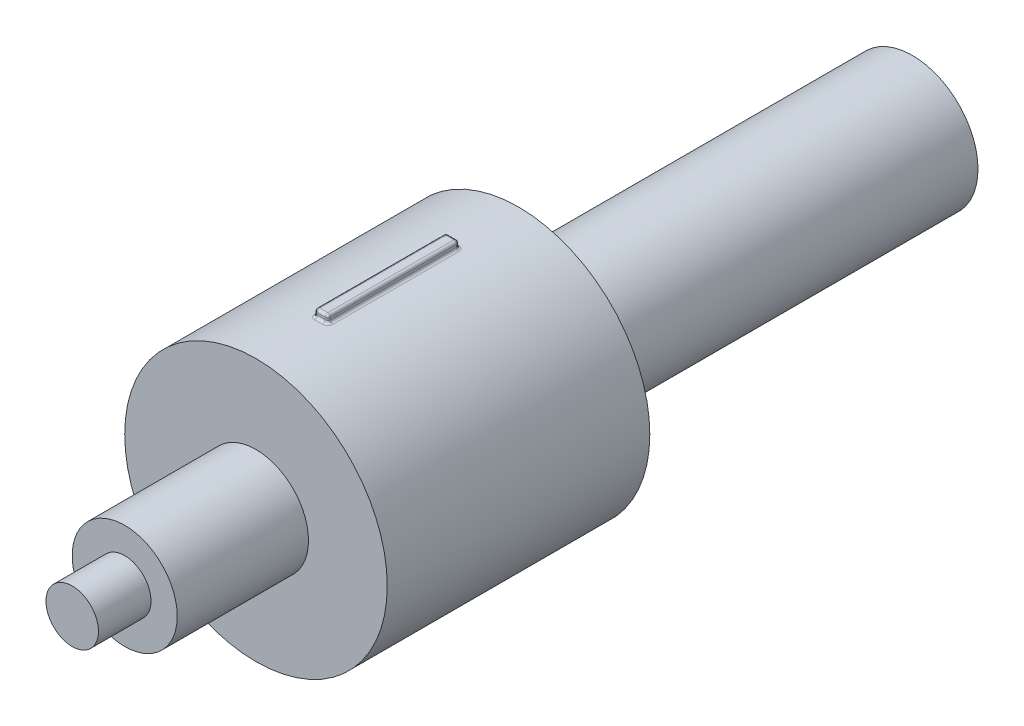
SolidWorks part; units mm, degrees
ref_plane "Front Plane" through (0, 0, 0) normal (0, 0, 1) x (1, 0, 0)
ref_plane "Top Plane" through (0, 0, 0) normal (0, 1, 0) x (1, 0, 0)
ref_plane "Right Plane" through (0, 0, 0) normal (1, 0, 0) x (0, 0, -1)
sketch "Sketch1" plane through (0, 0, 0) normal (0, 0, 1) x (1, 0, 0)
  circle A0 centre (0, 0) radius 5
extrude "Boss-Extrude1" add sketch "Sketch1" along normal blind 30
sketch "Sketch2" plane through (0, 0, 30) normal (0, 0, 1) x (1, 0, 0)
  circle A0 centre (0, 0) radius 10
extrude "Boss-Extrude2" add sketch "Sketch2" along normal blind 20
sketch "Sketch3" plane through (0, 0, 50) normal (0, 0, 1) x (1, 0, 0)
  circle A0 centre (0, 0) radius 4
extrude "Boss-Extrude3" add sketch "Sketch3" along normal blind 10
sketch "Sketch4" plane through (0, 0, 60) normal (0, 0, 1) x (1, 0, 0)
  circle A0 centre (0, 0) radius 2
extrude "Boss-Extrude4" add sketch "Sketch4" along normal blind 4
sketch "Sketch5" plane through (0, 0, 30) normal (0, 0, -1) x (-1, 0, 0)
  line L1 (-0.4647, 10.5602) -> (0.5353, 10.5602)
  line L2 (-0.4647, 10.5602) -> (-0.4647, 9.9637)
  line L4 (0.5353, 10.5602) -> (0.5353, 9.9602)
  line L5 (-0.4647, 10.5602) -> (0, 9.9746) construction
  line L6 (0, 9.9746) -> (0.5353, 10.5602) construction
  arc A0 (0.5353, 9.9602) -> (-0.4647, 9.9637) centre (0, 0) ccw
  point P3 (0, 9.9746)
  dimension "D1" = 1
  dimension "D2" = 0.6
extrude "Boss-Extrude5" add sketch "Sketch5" against normal blind 10 from offset 5 offset against normal yes
fillet "Fillet1" radius 0.2 12 edges at (0.4647, 9.9892, 40) (-0.0353, 9.9999, 45) (-0.0353, 9.9999, 35) (-0.5353, 9.9857, 40) (-0.5353, 10.2729, 45) (0.4647, 10.2747, 45) (-0.0353, 10.5602, 45) (-0.0353, 10.5602, 35) (0.4647, 10.2747, 35) (-0.5353, 10.2729, 35) (0.4647, 10.5602, 40) (-0.5353, 10.5602, 40)
